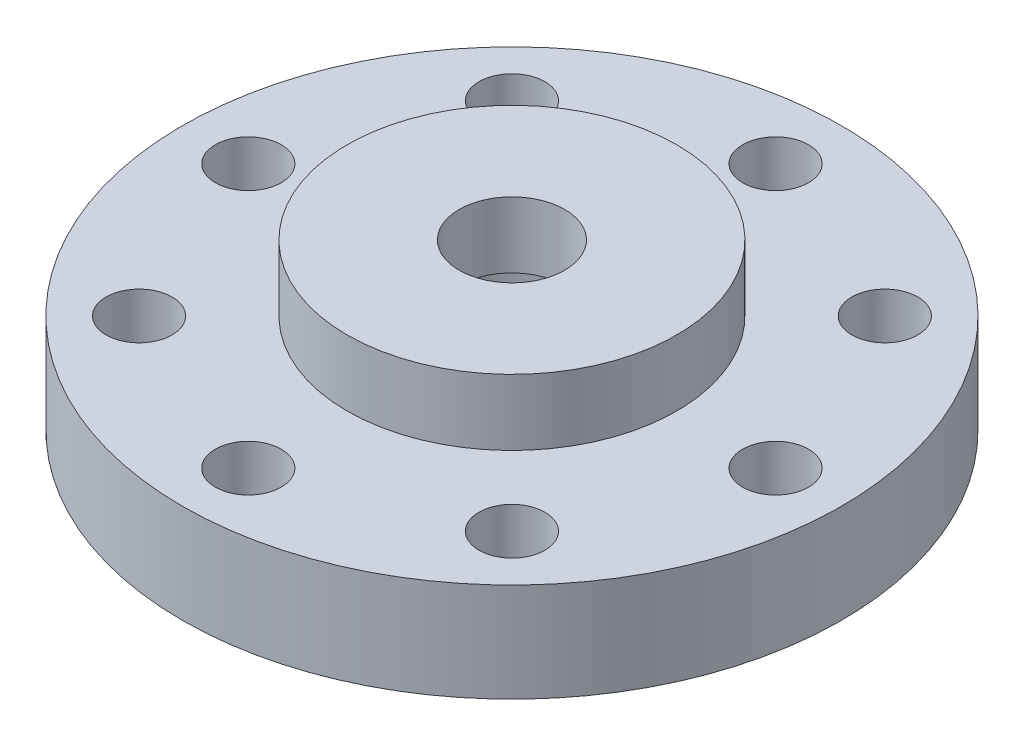
SolidWorks part; units mm, degrees
ref_plane "前视基准面" through (0, 0, 0) normal (0, 0, 1) x (1, 0, 0)
ref_plane "上视基准面" through (0, 0, 0) normal (0, 1, 0) x (1, 0, 0)
ref_plane "右视基准面" through (0, 0, 0) normal (1, 0, 0) x (0, 0, -1)
sketch "草图1" plane through (0, 0, 0) normal (0, 1, 0) x (1, 0, 0)
  circle A0 centre (0, 0) radius 10
  dimension "D1" = 20
extrude "凸台-拉伸1" add sketch "草图1" along normal blind 3
sketch "草图2" plane through (0, 3, 0) normal (0, 1, 0) x (1, 0, 0)
  circle A0 centre (0, 0) radius 5
  dimension "D1" = 10
extrude "凸台-拉伸2" add sketch "草图2" along normal blind 2
sketch "草图3" plane through (0, 0, 0) normal (0, -1, 0) x (1, 0, 0)
  circle A0 centre (0, 0) radius 1.6
  circle A1 centre (0, 8) radius 1
  circle A2 centre (5.6569, 5.6569) radius 1
  circle A3 centre (8, 0) radius 1
  circle A4 centre (5.6569, -5.6569) radius 1
  circle A5 centre (0, -8) radius 1
  circle A6 centre (-5.6569, -5.6569) radius 1
  circle A7 centre (-8, 0) radius 1
  circle A8 centre (-5.6569, 5.6569) radius 1
  point P22 (0, 0)
  dimension "D1" = 3.2
  dimension "D2" = 2
  dimension "D4" = 16
  dimension "D3" = 8
extrude "切除-拉伸1" cut sketch "草图3" against normal through all
sketch "草图4" plane through (0, 0, 0) normal (0, -1, 0) x (1, 0, 0)
  circle A0 centre (0, 0) radius 3
  dimension "D1" = 6
extrude "切除-拉伸2" cut sketch "草图4" against normal blind 3
